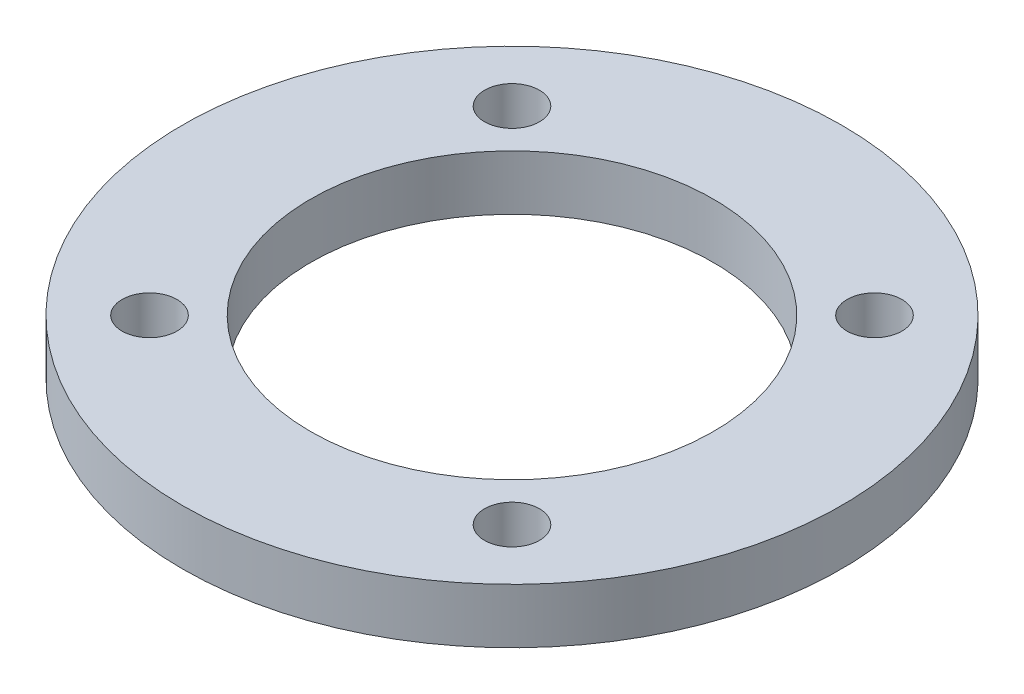
SolidWorks part; units mm, degrees
ref_plane "Front Plane" through (0, 0, 0) normal (0, 0, 1) x (1, 0, 0)
ref_plane "Top Plane" through (0, 0, 0) normal (0, 1, 0) x (1, 0, 0)
ref_plane "Right Plane" through (0, 0, 0) normal (1, 0, 0) x (0, 0, -1)
sketch "Sketch1" plane through (0, 0, 0) normal (0, 1, 0) x (1, 0, 0)
  line L0 (0, 0) -> (14, 0) construction
  line L1 (0, 0) -> (9.8995, 9.8995) construction
  circle A0 centre (0, 0) radius 11
  circle A1 centre (0, 0) radius 14 construction
  circle A2 centre (0, 0) radius 18
  circle A3 centre (9.8995, 9.8995) radius 1.5
  circle A4 centre (0, 0) radius 14 construction
  circle A5 centre (9.8995, -9.8995) radius 1.5
  circle A6 centre (0, 0) radius 14 construction
  circle A7 centre (-9.8995, -9.8995) radius 1.5
  circle A8 centre (0, 0) radius 14 construction
  circle A9 centre (-9.8995, 9.8995) radius 1.5
  point P21 (0, 0)
  dimension "D1" = 22
  dimension "D2" = 28
  dimension "D3" = 36
  dimension "D5" = 3
  dimension "D4" = 45
  dimension "D6" = 4
extrude "Boss-Extrude1" add sketch "Sketch1" along normal blind 3
